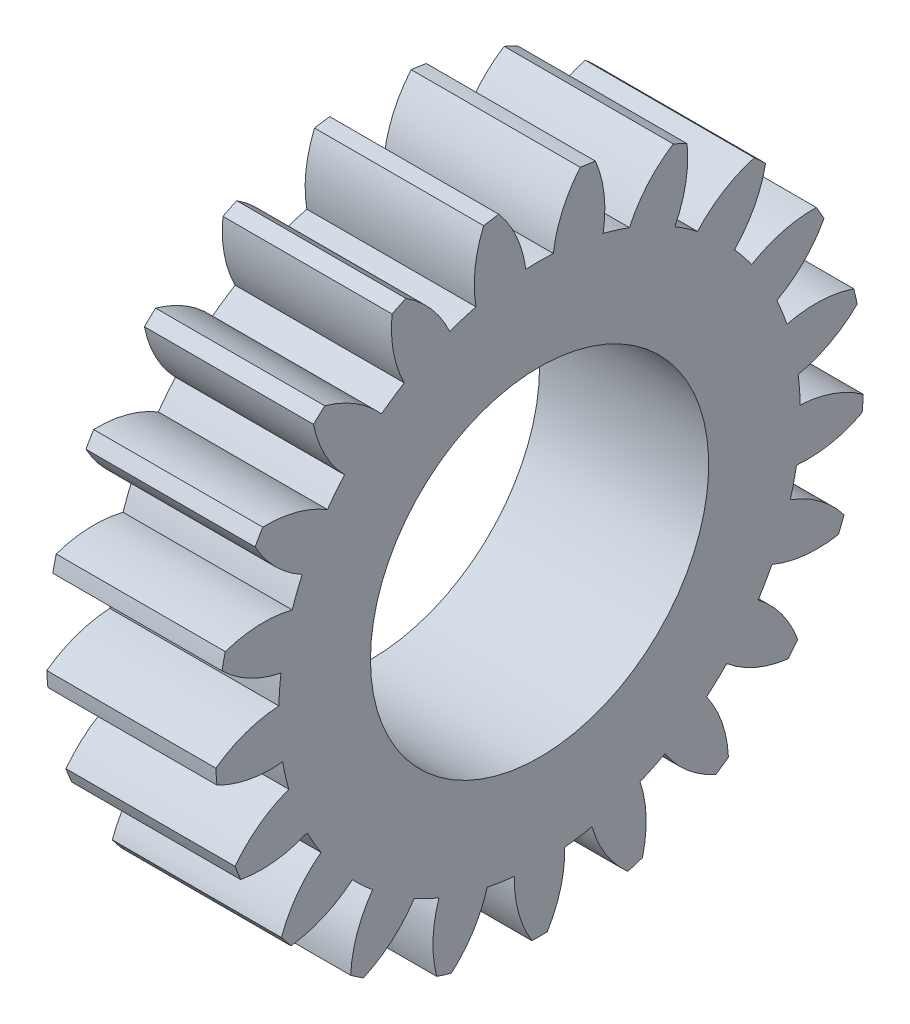
SolidWorks part; units mm, degrees
ref_plane "Plane1" through (0, 0, 0) normal (0, 0, 1) x (1, 0, 0)
ref_plane "Plane2" through (0, 0, 0) normal (0, 1, 0) x (1, 0, 0)
ref_plane "Plane3" through (0, 0, 0) normal (1, 0, 0) x (0, 0, -1)
sketch "HoldingSke" plane through (0, 0, 0) normal (0, 1, 0) x (1, 0, 0)
  line L0 (0, 0) -> (0.4668, -0.1792)
  line L1 (-15, 0) -> (100, 0) construction
  line L2 (0, 0) -> (-2.1039, 2.3779)
  line L3 (0, 0) -> (-11.863, 4.5341)
  line L4 (0, 0) -> (8.0624, 3.0949)
  line L5 (0, 0) -> (-46.8476, -17.4728)
  line L6 (0, 0) -> (-9.9476, -6.7116)
  line L7 (-2.1039, 2.3779) -> (8.6586, 51.2059)
  line L8 (-76.2, 54.61) -> (-72.9, 54.61)
  line L9 (-71.009, 38.7566) -> (-53.1078, 45.2721)
  line L10 (-76.2, 71.12) -> (104.1128, 71.12)
  line L11 (0, 0) -> (-12, 0)
  line L12 (-76.2, 101.6) -> (-76.133, 101.6)
  line L13 (24.9733, 27.94) -> (52.9518, 28.4284)
  line L14 (24.9733, 27.94) -> (24.9743, 27.94)
  line L15 (24.9733, 27.94) -> (100.4006, 29.5858)
  line L16 (-63.627, -2) -> (-12.827, -2)
  circle A0 centre (0, 0) radius 12
  circle A1 centre (0, 0) radius 18.499
  circle A2 centre (0, 0) radius 37.5
  circle A3 centre (0, 0) radius 12
  dimension "MHD" = 36.998
  dimension "Hub_dia" = 75
  dimension "Bore" = 24
  dimension "MBD" = 24
  dimension "Num_teeth" = 21
  dimension "Pitch" = 0.5
  dimension "Overall_len" = 50
  dimension "Show_teeth" = 21
  dimension "Thickness" = 12
  dimension "OAL" = 50.0001
  dimension "T_dim" = 3.3
  dimension "Ap" = 20
  dimension "H" = 19.05
  dimension "Pitch_radius" = 180.3128
  dimension "Width" = 12
  dimension "Backlash" = 0.067
  dimension "Addendum_fac" = 1
  dimension "Dedendum_fac" = 1.25
  dimension "Clearance_fac" = 0.25
  dimension "Dedendum_add" = 0.001
  dimension "Module" = 2
sketch "BasProSke" plane through (0, 0, 0) normal (0, 1, 0) x (1, 0, 0)
  line L0 (-10, 0) -> (60, 0) construction
  line L1 (0, 0) -> (0, 23)
  line L2 (0, 0) -> (12, 0)
  line L3 (12, 0) -> (12, 23)
  line L4 (12, 23) -> (0, 23)
  dimension "Thickness" = 12
  dimension "Diameter" = 46
revolve "Base-Revolve" add sketch "BasProSke" angle 360 about L0
sketch "TooCutSke" plane through (0, 0, 0) normal (1, 0, 0) x (0, 0, -1)
  line L1 (0, 0) -> (0, 107) construction
  line L2 (0, 0) -> (-1.6865, 20.9322) construction
  line L3 (0, 0) -> (-6.2448, 41.4315) construction
  line L4 (-1.6865, 20.9322) -> (-3.1224, 20.7157) construction
  arc A0 (0.9768, 18.4732) -> (-0.9768, 18.4732) centre (0, 0) ccw
  arc A1 (2.908, 22.841) -> (-2.908, 22.841) centre (0, 0) ccw
  circle A2 centre (0, 0) radius 21 construction
  circle A3 centre (0, 0) radius 19.7335 construction
  arc A4 (-0.9768, 18.4732) -> (-2.908, 22.841) centre (-9.308, 17.4004) ccw
  arc A5 (2.908, 22.841) -> (0.9768, 18.4732) centre (9.308, 17.4004) ccw
  dimension "Root_dia" = 36.998
  dimension "Overcut_dia" = 46.0508
  dimension "Pitch_dia" = 42
  dimension "Base_dia" = 39.4671
  dimension "Flank_rad" = 8.4
  dimension "Half_ang" = 8.571
  dimension "Half_CT" = 1.4521
extrude "ToothCut" cut sketch "TooCutSke" along normal through all
fillet "Breaks" [suppressed] radius 0.04
fillet "RootFillets" [suppressed] radius 0.501
pattern_circular "TeethCuts" count 21 every 17.143 about axis through (-10, 0, 0) along (1, 0, 0) of "ToothCut", "RootFillets", "Breaks"
sketch "HubNeaOneSke" plane through (0, 0, 0) normal (-1, 0, 0) x (0, 0, 1)
  circle A0 centre (0, 0) radius 18.499
  dimension "Diameter" = 36.998
extrude "HubNearOne" [suppressed] add sketch "HubNeaOneSke" along normal blind 38.0001
sketch "HubNeaBotSke" plane through (0, 0, 0) normal (-1, 0, 0) x (0, 0, 1)
  circle A0 centre (0, 0) radius 18.499
  dimension "Diameter" = 36.998
extrude "HubNearBoth" [suppressed] add sketch "HubNeaBotSke" along normal blind 19
ref_plane "FarPln" through (12, 0, 0) normal (1, 0, 0) x (0, 0, -1)
sketch "HubFarSke" plane through (12, 0, 0) normal (1, 0, 0) x (0, 0, -1)
  circle A0 centre (0, 0) radius 18.499
  dimension "Diameter" = 36.998
extrude "HubFar" [suppressed] add sketch "HubFarSke" along normal blind 19
sketch "BorSke" plane through (0, 0, 0) normal (1, 0, 0) x (0, 0, -1)
  circle A0 centre (0, 0) radius 12
  dimension "Diameter" = 24
extrude "Bore" cut sketch "BorSke" along normal mid plane 100.0001
sketch "KeySke" plane through (0, 0, 0) normal (1, 0, 0) x (0, 0, -1)
  line L0 (-4, 0) -> (-4, 15.3)
  line L1 (-4, 15.3) -> (4, 15.3)
  line L2 (4, 15.3) -> (4, 0)
  line L3 (0, 0) -> (0, 34) construction
  line L4 (-4, 0) -> (4, 0)
  dimension "Offset" = 15.3
  dimension "Width" = 8
extrude "Keyway" [suppressed] cut sketch "KeySke" along normal mid plane 100.0001
pattern_circular "Keyway2" [suppressed] count 2 every 90 about axis through (-10, 0, 0) along (1, 0, 0)
equation "' \"Module@HoldingSke\" = 6.35"
equation "' \"Num_teeth@HoldingSke\" = 12"
equation "' \"Ap@HoldingSke\" =  20"
equation "' \"Ap@HoldingSke\" = 20"
equation "' \"Width@HoldingSke\" = 0.5 * 25.4"
equation "' \"Hub_dia@HoldingSke\"= 1 * 25.4"
equation "' \"Hub_dia@HoldingSke\" = 1 * 25.4"
equation "' \"Overall_len@HoldingSke\" = 1.0 * 25.4"
equation "' \"Bore@HoldingSke\" = 0.75 * 25.4"
equation "' \"T_dim@HoldingSke\" = 0.1 * 25.4"
equation "' \"Width@KeySke\" = 0.25 * 25.4"
equation "' \"Show_teeth@HoldingSke\" = 13"
equation "' \"Backlash@HoldingSke\" = 0.009 * 25.4"
equation "' \"Addendum_fac@HoldingSke\" = 1.0"
equation "' \"Dedendum_fac@HoldingSke\" = 1.25"
equation "' \"Dedendum_add@HoldingSke\" = 0.00005 * 25.4"
equation "' \"Clearance_fac@HoldingSke\" = 0.25"
equation "\"Pitch@HoldingSke\" = 1 / \"Module@HoldingSke\""
equation "\"Overcut_dia@TooCutSke\" = (\"Num_teeth@HoldingSke\" + 2 * \"Addendum_fac@HoldingSke\") / \"Pitch@HoldingSke\" + 0.002 * 25.4"
equation "\"Pitch_dia@TooCutSke\" = \"Num_teeth@HoldingSke\" / \"Pitch@HoldingSke\""
equation "\"Base_dia@TooCutSke\" = \"Num_teeth@HoldingSke\" / \"Pitch@HoldingSke\" * cos((\"Ap@HoldingSke\"  * 3.14159265 / 180))"
equation "\"Root_dia@TooCutSke\" = (\"Num_teeth@HoldingSke\" + 2) / \"Pitch@HoldingSke\" - 2 * (\"Addendum_fac@HoldingSke\" + \"Dedendum_fac@HoldingSke\") / \"Pitch@HoldingSke\" - \"Dedendum_add@HoldingSke\" * 2"
equation "\"Half_ang@TooCutSke\" = 180 / \"Num_teeth@HoldingSke\""
equation "\"Half_CT@TooCutSke\" = \"Num_teeth@HoldingSke\" / \"Pitch@HoldingSke\" * sin((3.14159265 / 2 / \"Num_teeth@HoldingSke\")) / 2 - 7 * \"Backlash@HoldingSke\" / 4"
equation "\"Flank_rad@TooCutSke\" = \"Num_teeth@HoldingSke\" / \"Pitch@HoldingSke\" / 5"
equation "\"Radius@RootFillets\" = \"Clearance_fac@HoldingSke\" / \"Pitch@HoldingSke\" + \"Dedendum_add@HoldingSke\""
equation "\"Break_rad@Breaks\" = 0.02 / \"Pitch@HoldingSke\""
equation "\"Thickness@HoldingSke\" = \"Width@HoldingSke\""
equation "\"OAL@HoldingSke\" = \"Thickness@HoldingSke\""
equation "\"MHD@HoldingSke\" = (\"Num_teeth@HoldingSke\" + 2) / \"Pitch@HoldingSke\" - 2 * (\"Addendum_fac@HoldingSke\" + \"Dedendum_fac@HoldingSke\")  / \"Pitch@HoldingSke\" - \"Dedendum_add@HoldingSke\" * 2"
equation "\"MBD@HoldingSke\" = (\"Num_teeth@HoldingSke\" + 2) / \"Pitch@HoldingSke\" - 2 * (\"Addendum_fac@HoldingSke\" + \"Dedendum_fac@HoldingSke\")  / \"Pitch@HoldingSke\" - \"Dedendum_add@HoldingSke\" * 2 - 0.002 * 25.4"
equation "\"MHD@HoldingSke\" = ((sgn( \"MHD@HoldingSke\" - \"Hub_dia@HoldingSke\" )-1)*( \"MHD@HoldingSke\" - \"Hub_dia@HoldingSke\" ))/-2+ \"Hub_dia@HoldingSke\""
equation "\"MBD@HoldingSke\" = ((sgn( \"MBD@HoldingSke\" - \"Bore@HoldingSke\" )-1)*( \"MBD@HoldingSke\" - \"Bore@HoldingSke\" ))/-2+ \"Bore@HoldingSke\""
equation "\"OAL@HoldingSke\" = ((sgn( \"OAL@HoldingSke\" - \"Overall_len@HoldingSke\" )+1)*( \"OAL@HoldingSke\" - \"Overall_len@HoldingSke\" ))/2 + \"Overall_len@HoldingSke\" + 0.000002 * 25.4"
equation "\"Num_teeth@TeethCuts\" = int( \"Show_teeth@HoldingSke\" ) + 1"
equation "\"Num_teeth@TeethCuts\" = ((sgn( \"Num_teeth@TeethCuts\" - \"Num_teeth@HoldingSke\" )-1)*( \"Num_teeth@TeethCuts\" - \"Num_teeth@HoldingSke\" ))/-2+ \"Num_teeth@HoldingSke\""
equation "\"Num_teeth@TeethCuts\" = ((sgn( \"Num_teeth@TeethCuts\" - 2.0)+1)*( \"Num_teeth@TeethCuts\" - 2.0))/2 +2.0"
equation "\"Angle@TeethCuts\" = 360.0 / \"Num_teeth@HoldingSke\""
equation "\"Diameter@BasProSke\" = (\"Num_teeth@HoldingSke\" + 2 * \"Addendum_fac@HoldingSke\") / \"Pitch@HoldingSke\""
equation "\"Thickness@BasProSke\"  = \"Thickness@HoldingSke\""
equation "' \"Fillet_rad@BasProSke\" =  \"Thickness@HoldingSke\" * 0.05"
equation "' \"Fillet_rad@BasProSke\" = \"Thickness@HoldingSke\" * 0.05"
equation "\"MHD@HoldingSke\" = ((sgn( \"MHD@HoldingSke\" - \"Root_dia@TooCutSke\" )-1)*( \"MHD@HoldingSke\" - \"Root_dia@TooCutSke\" ))/-2+ \"Root_dia@TooCutSke\""
equation "\"Diameter@HubNeaOneSke\" = \"MHD@HoldingSke\""
equation "\"Length@HubNearOne\" = \"OAL@HoldingSke\" - \"Thickness@BasProSke\""
equation "\"Diameter@HubNeaBotSke\" = \"MHD@HoldingSke\""
equation "\"Length@HubNearBoth\" = ( \"OAL@HoldingSke\" - \"Thickness@BasProSke\" ) / 2.0"
equation "\"Thickness@FarPln\" = \"Thickness@BasProSke\""
equation "\"Diameter@HubFarSke\" = \"MHD@HoldingSke\""
equation "\"Length@HubFar\" = ( \"OAL@HoldingSke\" - \"Thickness@BasProSke\" ) / 2.0"
equation "\"Diameter@BorSke\" = \"MBD@HoldingSke\""
equation "\"D1@Bore\" = \"OAL@HoldingSke\" * 2.0"
equation "\"D1@Keyway\" = \"OAL@HoldingSke\" * 2.0"
equation "\"Offset@KeySke\" = \"T_dim@HoldingSke\" + \"MBD@HoldingSke\" / 2.0"
